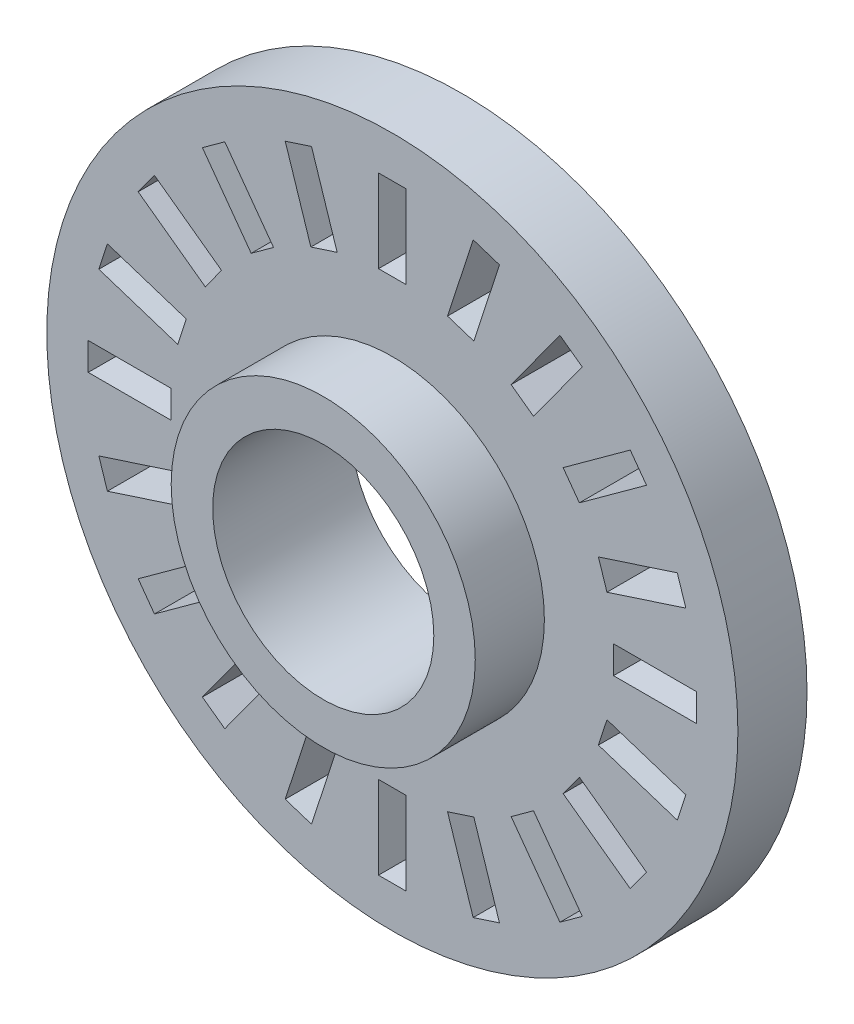
SolidWorks part; units mm, degrees
ref_plane "Front" through (0, 0, 0) normal (0, 0, 1) x (1, 0, 0)
ref_plane "Top" through (0, 0, 0) normal (0, 1, 0) x (1, 0, 0)
ref_plane "Right" through (0, 0, 0) normal (1, 0, 0) x (0, 0, -1)
sketch "草图1" plane through (0, 0, 0) normal (0, 0, 1) x (1, 0, 0)
  circle A0 centre (0, 0) radius 25
  circle A1 centre (0, 0) radius 8
  dimension "D1" = 50
  dimension "D2" = 16
extrude "凸台-拉伸1" add sketch "草图1" along normal blind 5
sketch "草图2" plane through (0, 0, 5) normal (0, 0, 1) x (1, 0, 0)
  circle A0 centre (0, 0) radius 8 construction
  circle A1 centre (0, 0) radius 8
  circle A2 centre (0, 0) radius 11
  dimension "D1" = 22
extrude "凸台-拉伸2" add sketch "草图2" along normal blind 5
sketch "草图3" plane through (0, 0, 5) normal (0, 0, 1) x (1, 0, 0)
  line L1 (-1, 16) -> (1, 16)
  line L2 (-1, 16) -> (-1, 22)
  line L3 (-1, 22) -> (1, 22)
  line L4 (1, 16) -> (1, 22)
  line L5 (-1, 16) -> (1, 22) construction
  line L6 (-1, 22) -> (1, 16) construction
  point P0 (0, 19)
  point P5 (0, 16.5373)
  point P7 (0, 0)
  dimension "D1" = 2
  dimension "D2" = 6
  dimension "D3" = 19
extrude "切除-拉伸1" cut sketch "草图3" against normal blind 5
pattern_circular "阵列(圆周)1" count 20 over 360 about axis through (0, 0, 0) along (0, 0, 1) of "切除-拉伸1"
